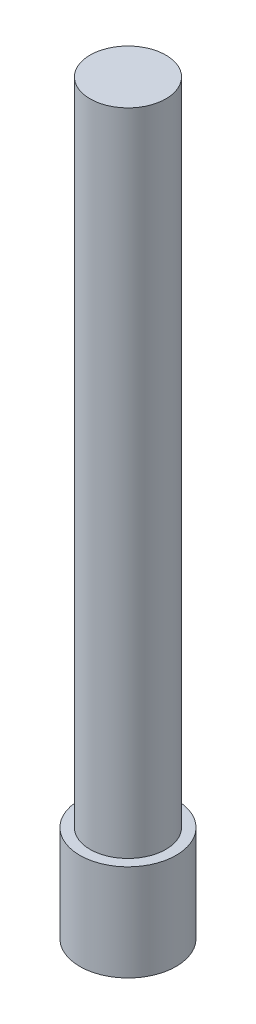
SolidWorks part; units mm, degrees
ref_plane "Front Plane" through (0, 0, 0) normal (0, 0, 1) x (1, 0, 0)
ref_plane "Top Plane" through (0, 0, 0) normal (0, 1, 0) x (1, 0, 0)
ref_plane "Right Plane" through (0, 0, 0) normal (1, 0, 0) x (0, 0, -1)
sketch "Sketch1" plane through (0, 0, 0) normal (0, 1, 0) x (1, 0, 0)
  circle A0 centre (0, 0) radius 1.025
  circle A1 centre (0, 0) radius 2
  dimension "D1" = 2.05
  dimension "D2" = 4
extrude "Boss-Extrude1" add sketch "Sketch1" along normal blind 3
sketch "Sketch2" plane through (0, 3, 0) normal (0, 1, 0) x (1, 0, 0)
  circle A0 centre (0, 0) radius 2
  circle A1 centre (0, 0) radius 2 construction
extrude "Boss-Extrude2" add sketch "Sketch2" along normal blind 1
sketch "Sketch3" plane through (0, 4, 0) normal (0, 1, 0) x (1, 0, 0)
  circle A0 centre (0, 0) radius 1.575
  dimension "D1" = 3.15
extrude "Boss-Extrude3" add sketch "Sketch3" along normal blind 27
